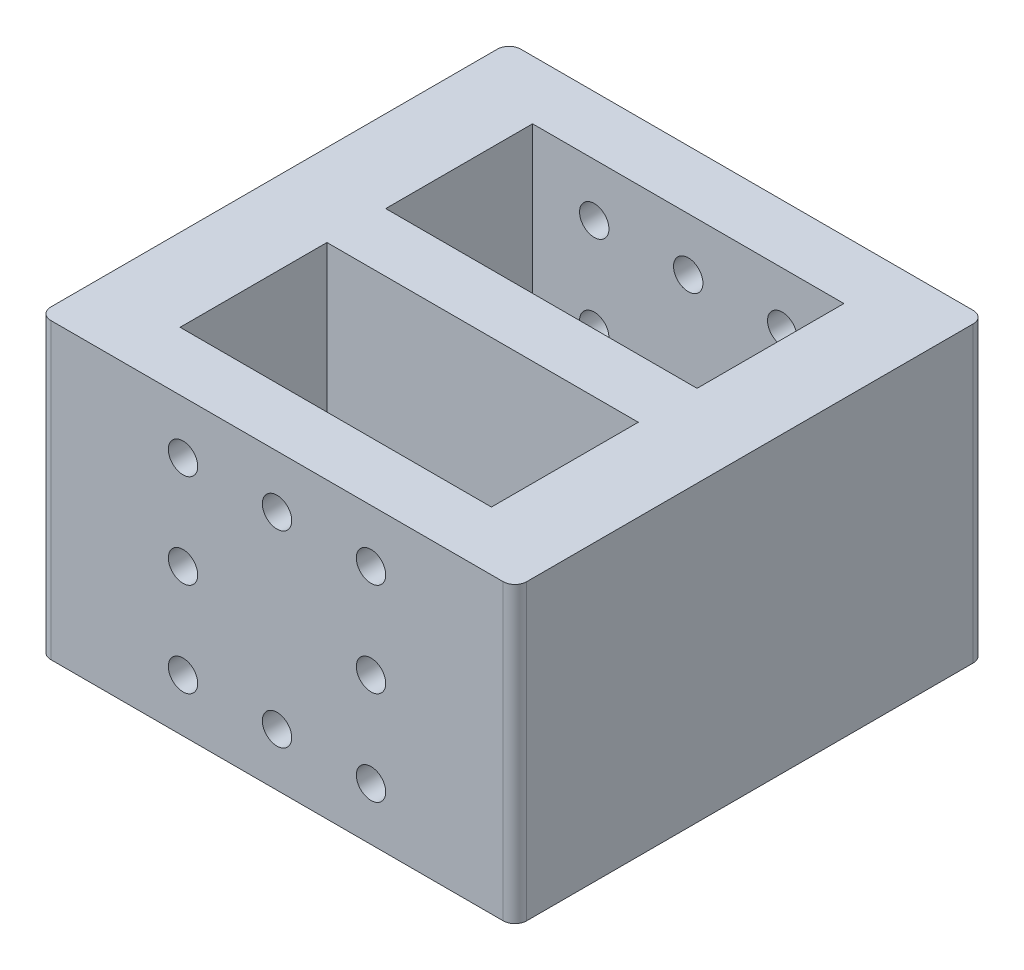
SolidWorks part; units mm, degrees
ref_plane "Front Plane" through (0, 0, 0) normal (0, 0, 1) x (1, 0, 0)
ref_plane "Top Plane" through (0, 0, 0) normal (0, 1, 0) x (1, 0, 0)
ref_plane "Right Plane" through (0, 0, 0) normal (1, 0, 0) x (0, 0, -1)
sketch "Sketch1" plane through (0, 0, 0) normal (0, 0, 1) x (1, 0, 0)
  line L1 (0, 0) -> (40.5, 0)
  line L2 (0, 0) -> (0, 25)
  line L3 (0, 25) -> (40.5, 25)
  line L4 (40.5, 0) -> (40.5, 25)
  dimension "D1" = 40.5
  dimension "D2" = 25
extrude "Boss-Extrude1" add sketch "Sketch1" along normal blind 40
sketch "Sketch2" plane through (0, 0, 40) normal (0, 0, 1) x (1, 0, 0)
  line L0 (0, 25) -> (0, 0) construction
  line L1 (7, 25) -> (33.5, 25)
  line L2 (7, 25) -> (7, 0)
  line L3 (7, 0) -> (33.5, 0)
  line L4 (33.5, 25) -> (33.5, 0)
  line L5 (0, 0) -> (40.5, 0) construction
  line L6 (40.5, 0) -> (40.5, 25) construction
  point P10 (33.5, 12.5)
  point P12 (0, 12.5)
  point P13 (7, 12.5)
  dimension "D1" = 7
  dimension "D2" = 25
  dimension "D3" = 7
extrude "Cut-Extrude1" cut sketch "Sketch2" against normal blind 30 from offset 5 offset against normal yes
fillet "Fillet1" radius 1 2 edges at (40.5, 12.5, 0) (0, 12.5, 0)
sketch "Sketch3" plane through (0, 0, 5) normal (0, 0, 1) x (1, 0, 0)
  line L0 (7, 25) -> (7, 0) construction
  line L1 (33.5, 25) -> (7, 25) construction
  circle A0 centre (12.25, 4.5) radius 1.25
  circle A1 centre (20.25, 4.5) radius 1.25
  circle A3 centre (12.25, 12.5) radius 1.25
  circle A4 centre (12.25, 20.5) radius 1.25
  circle A5 centre (20.25, 20.5) radius 1.25
  circle A6 centre (28.25, 4.5) radius 1.25
  circle A7 centre (28.25, 12.5) radius 1.25
  circle A8 centre (28.25, 20.5) radius 1.25
  circle A9 centre (20.25, 12.5) radius 1.25 [skipped]
  dimension "D1" = 2.5
  dimension "D2" = 5.25
  dimension "D3" = 4.5
  dimension "D6" = 8
  dimension "D7" = 8
  dimension "D4" = 3
  dimension "D5" = 3
extrude "Cut-Extrude2" cut sketch "Sketch3" against normal blind 5 and the other way blind 35
sketch "Sketch6" plane through (40.5, 0, 0) normal (1, 0, 0) x (0, 0, -1)
  line L0 (-40, 25) -> (-1, 25) construction
  line L1 (-22.5, 25) -> (-17.5, 25)
  line L2 (-22.5, 25) -> (-22.5, 0)
  line L3 (-22.5, 0) -> (-17.5, 0)
  line L4 (-17.5, 25) -> (-17.5, 0)
  line L5 (0, 25) -> (0, 0) construction
  dimension "D1" = 25
  dimension "D2" = 5
  dimension "D3" = 0
  dimension "D4" = 17.5
fillet "Fillet2" radius 1 2 edges at (0, 12.5, 40) (40.5, 12.5, 40)
extrude "Boss-Extrude3" add sketch "Sketch6" against normal blind 40.5 contours L3 L4 L1 L2
